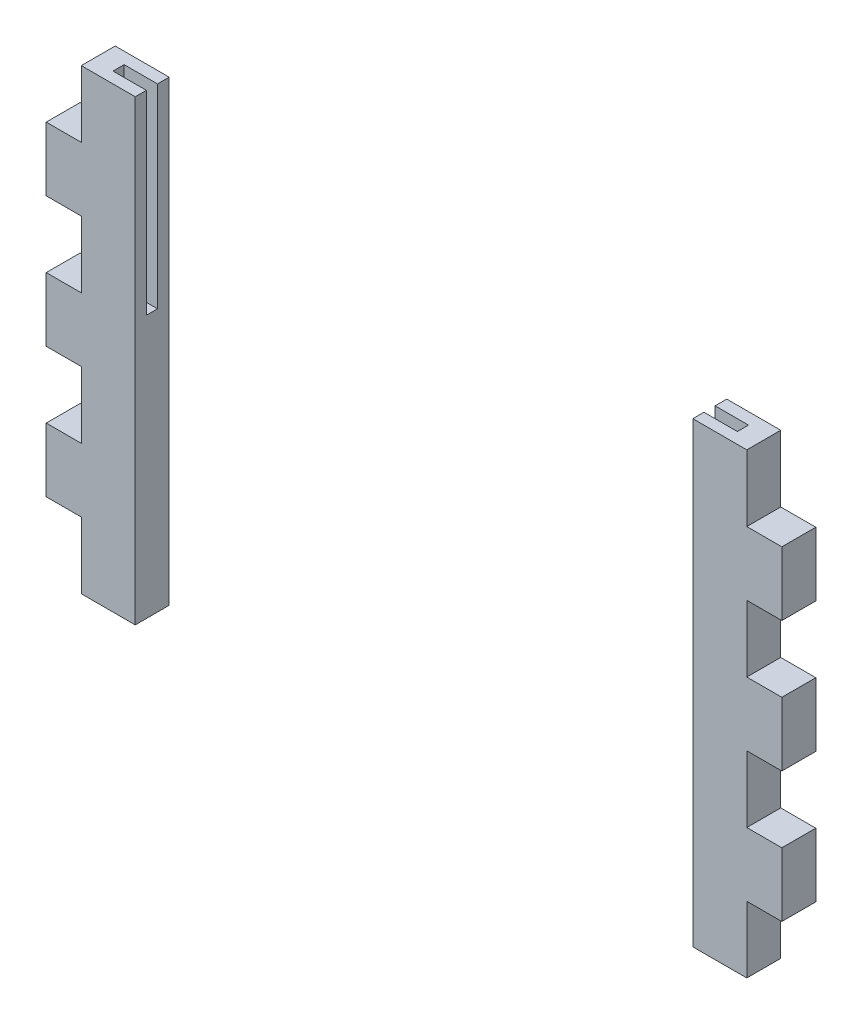
SolidWorks part; units mm, degrees
ref_plane "Plan de face" through (0, 0, 0) normal (0, 0, 1) x (1, 0, 0)
ref_plane "Plan de dessus" through (0, 0, 0) normal (0, 1, 0) x (1, 0, 0)
ref_plane "Plan de droite" through (0, 0, 0) normal (1, 0, 0) x (0, 0, -1)
sketch "Esquisse1" plane through (0, 0, 0) normal (0, 0, 1) x (1, 0, 0)
  line L1 (-163.0852, 185.3139) -> (167.4148, 185.3139)
  line L2 (-163.0852, 185.3139) -> (-163.0852, -20.1861)
  line L3 (-163.0852, -20.1861) -> (167.4148, -20.1861)
  line L4 (167.4148, 185.3139) -> (167.4148, -20.1861)
  line L5 (-123.0852, -20.1861) -> (127.4148, -20.1861)
  line L6 (-123.0852, -20.1861) -> (-123.0852, 185.3139)
  line L7 (-123.0852, 185.3139) -> (127.4148, 185.3139)
  line L8 (127.4148, -20.1861) -> (127.4148, 185.3139)
  line L9 (-123.0852, 185.3139) -> (-123.0852, 50.3139) construction
extrude "Boss.-Extru.1" add sketch "Esquisse1" along normal blind 15.25 contours L3 L6 L1 L2 | L8 L3 L4 L1
sketch "Esquisse2" plane through (0, 0, 0) normal (0, 0, -1) x (-1, 0, 0)
  line L0 (-2.1648, -20.1861) -> (-2.1648, 185.3139) construction
  line L1 (123.0852, 185.3139) -> (138.0852, 185.3139)
  line L2 (123.0852, 185.3139) -> (123.0852, 97.8139)
  line L3 (123.0852, 97.8139) -> (138.0852, 97.8139)
  line L4 (138.0852, 185.3139) -> (138.0852, 97.8139)
  line L5 (-127.4148, 185.3139) -> (-142.4148, 185.3139)
  line L6 (-127.4148, 185.3139) -> (-127.4148, 97.8139)
  line L7 (-127.4148, 97.8139) -> (-142.4148, 97.8139)
  line L8 (-142.4148, 185.3139) -> (-142.4148, 97.8139)
  line L9 (-127.4148, 185.3139) -> (123.0852, 185.3139)
  line L11 (132.8352, -20.1861) -> (-137.1648, -20.1861) construction
  line L15 (163.0852, 185.3139) -> (123.0852, 185.3139) construction
  point P16 (-2.1648, 185.3139)
  dimension "D1" = 15
  dimension "D2" = 87.5
extrude "Enlèv. mat.-Extru.1" cut sketch "Esquisse2" against normal blind 5 from surface at -5.25
sketch "Esquisse3" plane through (0, 0, 0) normal (0, 0, -1) x (-1, 0, 0)
  line L0 (163.0852, 185.3139) -> (163.0852, -20.1861) construction
  line L1 (163.0852, 185.3139) -> (147.3352, 185.3139)
  line L2 (163.0852, 185.3139) -> (163.0852, 155.4567)
  line L3 (163.0852, 155.4567) -> (147.3352, 155.4567)
  line L4 (147.3352, 185.3139) -> (147.3352, 155.4567)
  line L5 (147.3352, 126.7662) -> (163.0852, 126.7662)
  line L6 (147.3352, 126.7662) -> (147.3352, 96.9091)
  line L7 (147.3352, 96.9091) -> (163.0852, 96.9091)
  line L8 (163.0852, 126.7662) -> (163.0852, 96.9091)
  line L9 (163.0852, 38.3615) -> (147.3352, 38.3615) construction
  line L10 (147.3352, 68.2186) -> (163.0852, 68.2186)
  line L11 (147.3352, 68.2186) -> (147.3352, 38.3615)
  line L12 (147.3352, 38.3615) -> (163.0852, 38.3615)
  line L13 (163.0852, 68.2186) -> (163.0852, 38.3615)
  line L14 (147.3352, 9.671) -> (163.0852, 9.671)
  line L15 (147.3352, 9.671) -> (147.3352, -20.1861)
  line L16 (147.3352, -20.1861) -> (163.0852, -20.1861)
  line L17 (163.0852, 9.671) -> (163.0852, -20.1861)
  line L18 (163.0852, 96.9091) -> (147.3352, 96.9091) construction
  dimension "D1" = 0
  dimension "D2" = 0
extrude "Enlèv. mat.-Extru.2" cut sketch "Esquisse3" against normal up to next (15.25 mm away)
ref_plane "Plan1" through (2.1648, 0, 0) normal (-1, 0, 0) x (0, 0, 1)
mirror "Symétrie3" about plane through (2.1648, 0, 0) normal (-1, 0, 0) of "Enlèv. mat.-Extru.2"
